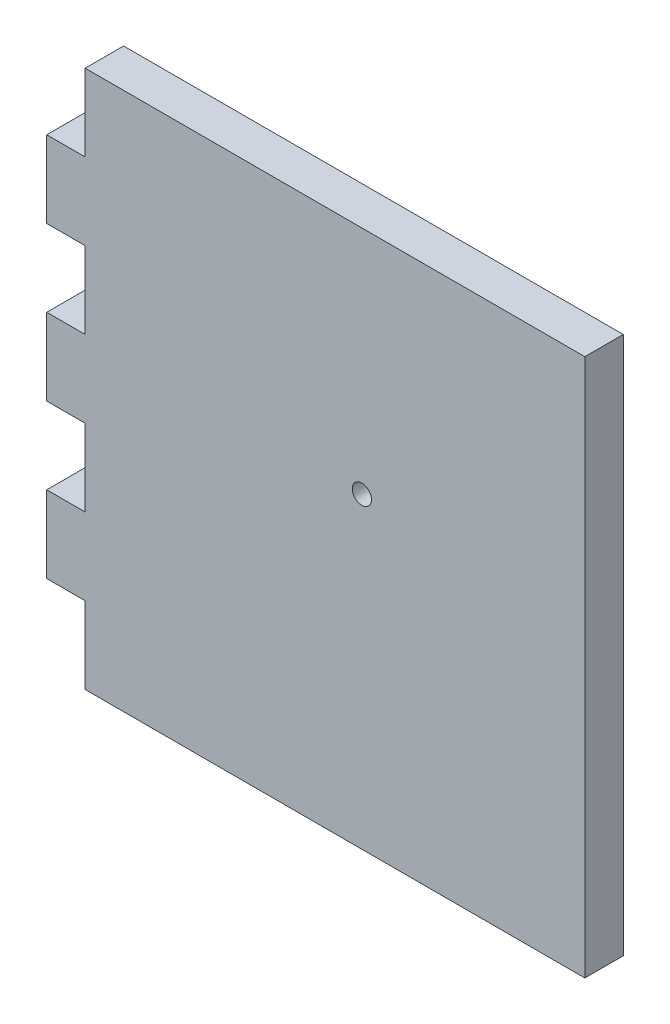
SolidWorks part; units mm, degrees
ref_plane "Front Plane" through (0, 0, 0) normal (0, 0, 1) x (1, 0, 0)
ref_plane "Top Plane" through (0, 0, 0) normal (0, 1, 0) x (1, 0, 0)
ref_plane "Right Plane" through (0, 0, 0) normal (1, 0, 0) x (0, 0, -1)
sketch "Sketch1" plane through (0, 0, 0) normal (0, 0, 1) x (1, 0, 0)
  line L1 (0, 0) -> (177.8, 0)
  line L2 (0, 0) -> (0, -177.8)
  line L3 (0, -177.8) -> (177.8, -177.8)
  line L4 (177.8, 0) -> (177.8, -177.8)
  dimension "D1" = 177.8
  dimension "D2" = 177.8
extrude "Boss-Extrude1" add sketch "Sketch1" along normal blind 12.7
sketch "Sketch2" plane through (0, 0, 12.7) normal (0, 0, 1) x (1, 0, 0)
  line L4 (0, 0) -> (0, -177.8)
  line L5 (0, -177.8) -> (177.8, -177.8)
  line L6 (177.8, -177.8) -> (177.8, 0)
  line L7 (177.8, 0) -> (0, 0)
  line L8 (0, 0) -> (0, -177.8)
  line L9 (0, -177.8) -> (177.8, -177.8)
  line L10 (177.8, -177.8) -> (177.8, 0)
  line L11 (177.8, 0) -> (0, 0)
  circle A0 centre (104.14, -76.2) radius 3.175
  dimension "D3" = 6.35
  dimension "D2" = 104.14
  dimension "D4" = 101.6
  dimension "D1" = 0
extrude "Cut-Extrude3" cut sketch "Sketch2" against normal through all contours A0
sketch "Sketch4" plane through (0, 0, 12.7) normal (0, 0, 1) x (1, 0, 0)
  line L0 (0, 0) -> (0, -177.8) construction
  line L1 (0, 0) -> (12.7, 0)
  line L2 (0, 0) -> (0, -25.4)
  line L3 (0, -25.4) -> (12.7, -25.4)
  line L4 (12.7, 0) -> (12.7, -25.4)
  line L5 (0, -50.8) -> (12.7, -50.8)
  line L6 (0, -50.8) -> (0, -76.2)
  line L7 (0, -76.2) -> (12.7, -76.2)
  line L8 (12.7, -50.8) -> (12.7, -76.2)
  line L9 (0, -76.2) -> (177.8, -76.2) construction
  line L10 (177.8, -177.8) -> (177.8, 0) construction
  line L12 (0, -101.6) -> (12.7, -101.6)
  line L13 (0, -101.6) -> (0, -127)
  line L14 (0, -127) -> (12.7, -127)
  line L15 (12.7, -101.6) -> (12.7, -127)
  line L16 (0, -177.8) -> (12.7, -177.8)
  line L17 (0, -177.8) -> (0, -152.4)
  line L18 (0, -152.4) -> (12.7, -152.4)
  line L19 (12.7, -177.8) -> (12.7, -152.4)
  dimension "D1" = 25.4
  dimension "D2" = 12.7
  dimension "D3" = 25.4
  dimension "D4" = 12.7
  dimension "D5" = 25.4
  dimension "D6" = 25.4
  dimension "D7" = 25.4
  dimension "D8" = 12.7
  dimension "D9" = 25.4
extrude "Cut-Extrude4" cut sketch "Sketch4" against normal through all contours L2 L1 L4 L3 | L6 L5 L8 L7 | L13 L12 L15 L14 | L17 L16 L19 L18
